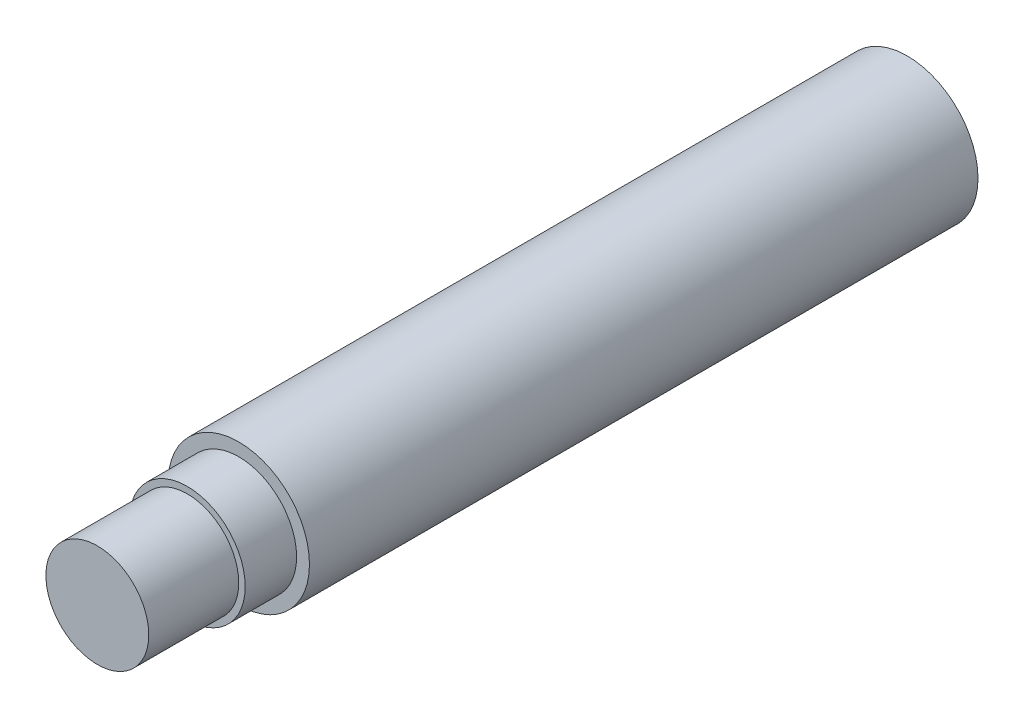
SolidWorks part; units mm, degrees
ref_plane "Front Plane" through (0, 0, 0) normal (0, 0, 1) x (1, 0, 0)
ref_plane "Top Plane" through (0, 0, 0) normal (0, 1, 0) x (1, 0, 0)
ref_plane "Right Plane" through (0, 0, 0) normal (1, 0, 0) x (0, 0, -1)
sketch "Sketch1" plane through (0, 0, 0) normal (1, 0, 0) x (0, 0, -1)
  line L0 (0, 0) -> (22.6707, 0)
  line L1 (63, 2.5) -> (63, 5.5)
  line L2 (63, 5.5) -> (11, 5.5)
  line L3 (11, 5.5) -> (11, 4.5)
  line L4 (11, 4.5) -> (7, 4.5)
  line L5 (7, 4.5) -> (7, 4)
  line L6 (7, 4) -> (0, 4)
  line L7 (0, 4) -> (0, 0)
  line L8 (22.6707, 0) -> (24, 2.5)
  line L9 (24, 2.5) -> (63, 2.5)
  dimension "D1" = 4
  dimension "D2" = 4.5
  dimension "D3" = 5.5
  dimension "D4" = 63
  dimension "D5" = 7
  dimension "D6" = 4
  dimension "D7" = 2.5
  dimension "D8" = 39
  dimension "D9" = 118
revolve "Revolve1" add sketch "Sketch1" angle 360 about L0
hole_wizard "Tap Drill for M8x1.0 Tap1" positions "Sketch3" profile "Sketch2" hole size "M8x1.0" standard "ANSI Metric"
sketch "Sketch3" plane through (0, 0, -63) normal (0, 0, -1) x (-1, 0, 0)
  point P0 (0, 0)
sketch "Sketch2" plane through (0, 0, -63) normal (1, 0, 0) x (0, 1, 0)
  line L0 (0, 0) -> (0, 8.103)
  line L1 (0, 8.103) -> (3.5, 6)
  line L2 (3.5, 6) -> (3.5, 0)
  line L5 (3.5, 0) -> (0, 0)
  line L10 (0, 8.103) -> (-3.5, 6) construction
  line L11 (0, -6.35) -> (0, 107.95) construction
  dimension "Hole Dia." = 7
  dimension "Hole Depth" = 6
  dimension "Drill Angle" = 118
